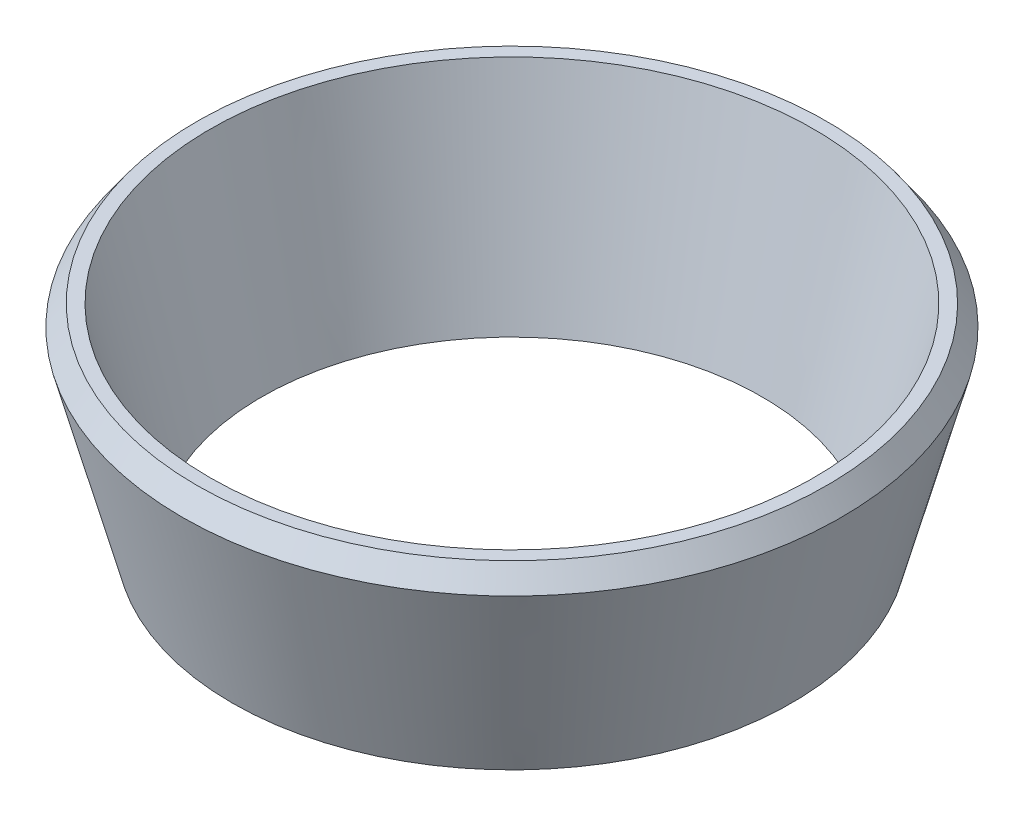
SolidWorks part; units mm, degrees
ref_plane "Front Plane" through (0, 0, 0) normal (0, 0, 1) x (1, 0, 0)
ref_plane "Top Plane" through (0, 0, 0) normal (0, 1, 0) x (1, 0, 0)
ref_plane "Right Plane" through (0, 0, 0) normal (1, 0, 0) x (0, 0, -1)
sketch "Sketch1" plane through (0, 0, 0) normal (0, 0, 1) x (1, 0, 0)
  line L0 (0, 93.3731) -> (0, -93.3731) construction
  line L2 (20.5, 2.1476) -> (17, -11.8524)
  line L4 (20.5, 2.1476) -> (21.4, 2.1476)
  line L6 (21.4, 2.1476) -> (22.3793, 0.758)
  line L9 (17, -11.8524) -> (19, -11.8524)
  line L11 (20.5, 2.1476) -> (21.4, 2.1476)
  line L14 (22.3793, 0.758) -> (19, -11.8524)
  point P4 (0, 0)
  dimension "D4" = 0.9
  dimension "D5" = 1.7
  dimension "D6" = 2
revolve "Revolve1" add sketch "Sketch1" angle 360 about L0
